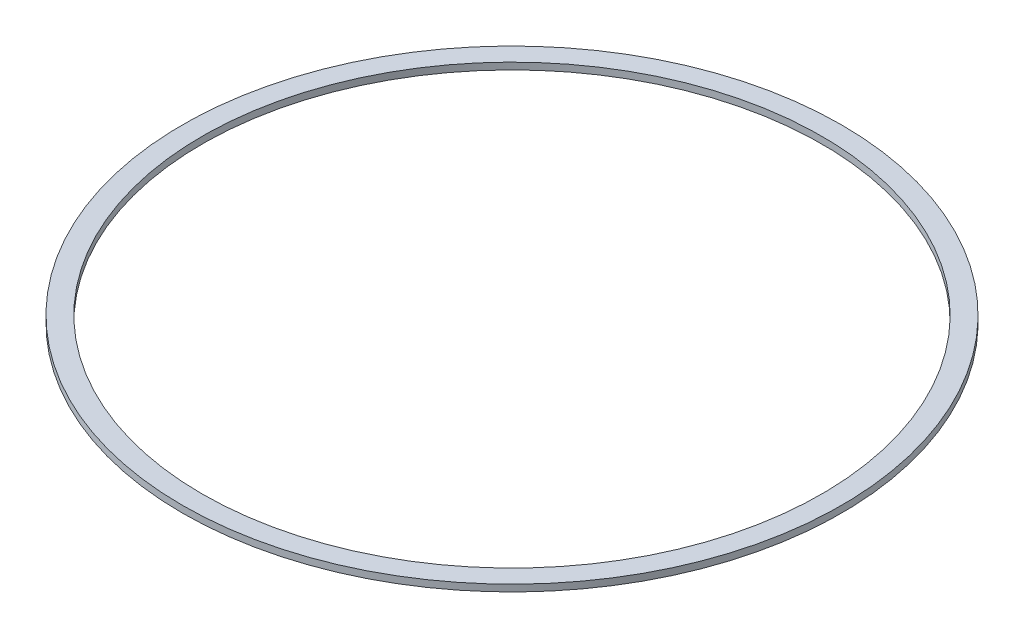
SolidWorks part; units mm, degrees
material "Rubber"
ref_plane "Front Plane" through (0, 0, 0) normal (0, 0, 1) x (1, 0, 0)
ref_plane "Top Plane" through (0, 0, 0) normal (0, 1, 0) x (1, 0, 0)
ref_plane "Right Plane" through (0, 0, 0) normal (1, 0, 0) x (0, 0, -1)
sketch "Эскиз1" plane through (0, 0, 0) normal (0, 1, 0) x (1, 0, 0)
  circle A0 centre (0, 0) radius 27.5
  circle A1 centre (0, 0) radius 29.25
  dimension "D1" = 55
  dimension "D2" = 58.5
extrude "Бобышка-Вытянуть1" add sketch "Эскиз1" along normal blind 0.6
